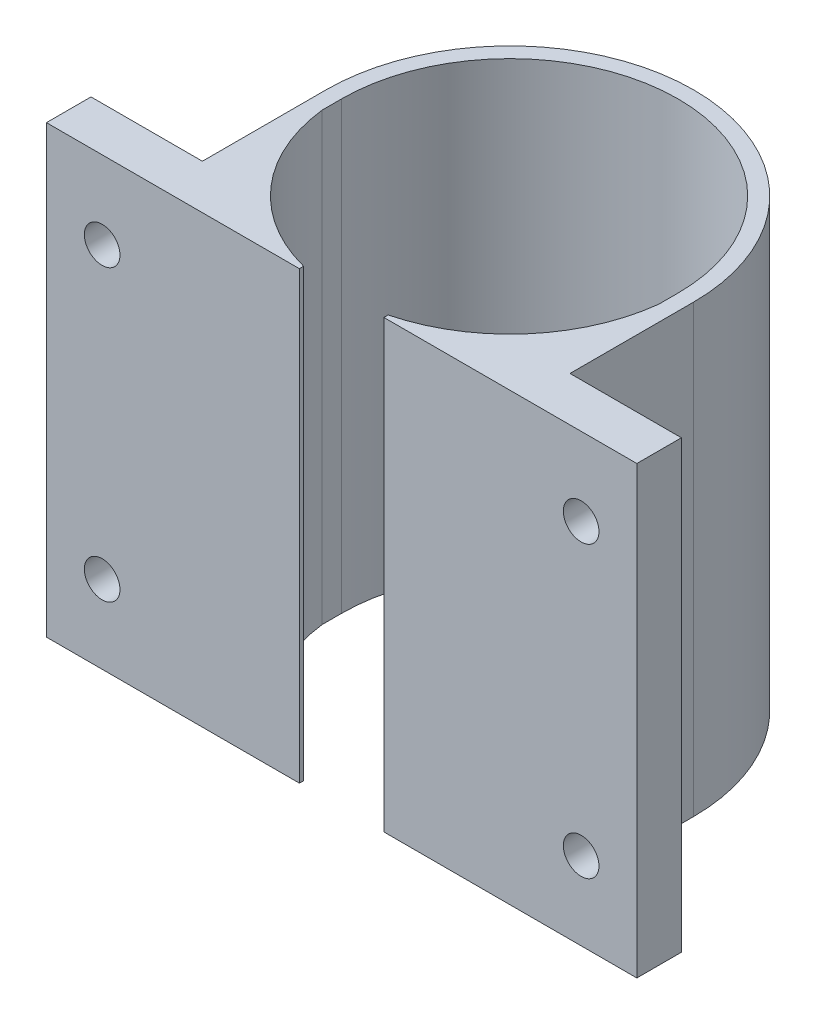
SolidWorks part; units mm, degrees
ref_plane "Front Plane" through (0, 0, 0) normal (0, 0, 1) x (1, 0, 0)
ref_plane "Top Plane" through (0, 0, 0) normal (0, 1, 0) x (1, 0, 0)
ref_plane "Right Plane" through (0, 0, 0) normal (1, 0, 0) x (0, 0, -1)
sketch "Sketch3" plane through (0, 0, 0) normal (0, 1, 0) x (1, 0, 0)
  line L0 (-16.5, 0) -> (-16.5, -15.1)
  line L2 (16.5, -15.1) -> (16.5, 0)
  line L3 (15.1, 0) -> (15.1, -15.1)
  line L4 (-15.1, 0) -> (-15.1, -15.1)
  line L5 (0, -15.1) -> (-16.5, -15.1)
  line L6 (-16.5, -15.1) -> (16.5, -15.1)
  arc A0 (15.1, 0) -> (-15.1, 0) centre (0, 0) ccw
  arc A1 (16.5, 0) -> (-16.5, 0) centre (0, 0) ccw
extrude "Boss-Extrude3" add sketch "Sketch3" along normal blind 40
sketch "Sketch8" plane through (16.5, 0, 0) normal (1, 0, 0) x (0, 0, -1)
  line L0 (-15.1, 40) -> (0, 40) construction
  line L1 (-15.1, 0) -> (-11.1, 0)
  line L2 (-15.1, 0) -> (-15.1, 40)
  line L3 (-15.1, 40) -> (-11.1, 40)
  line L4 (-11.1, 0) -> (-11.1, 40)
extrude "Boss-Extrude6" add sketch "Sketch8" along normal blind 10
sketch "Sketch9" plane through (-16.5, 0, 0) normal (-1, 0, 0) x (0, 0, 1)
  line L0 (0, 0) -> (15.1, 0) construction
  line L1 (15.1, 40) -> (11.1, 40)
  line L2 (15.1, 40) -> (15.1, 0)
  line L3 (15.1, 0) -> (11.1, 0)
  line L4 (11.1, 40) -> (11.1, 0)
extrude "Boss-Extrude7" add sketch "Sketch9" along normal blind 10
sketch "Sketch10" plane through (0, 0, 0) normal (0, -1, 0) x (-1, 0, 0)
  line L7 (15.1, -15.1) -> (15.1, -1.7407)
  line L9 (15.1, -15.1) -> (1.7407, -15.1)
  line L10 (3.7913, -15.1) -> (3.7913, -14.7196)
  line L11 (15.1, 0) -> (15.1, -15.1) construction
  line L12 (0, 0) -> (0, 15.1) construction
  line L13 (-3.7913, -15.1) -> (-3.7913, -14.7196)
  line L14 (-15.1, -15.1) -> (-1.7407, -15.1)
  line L15 (-15.1, -15.1) -> (-15.1, -1.7407)
  arc A1 (1.7407, -15.1) -> (15.1, -1.7407) centre (0, 0) ccw
  arc A2 (15.1, 0) -> (-15.1, 0) centre (0, 0) ccw construction
  arc A3 (-1.7407, -15.1) -> (-15.1, -1.7407) centre (0, 0) cw
extrude "Boss-Extrude9" add sketch "Sketch10" against normal blind 40 contours L13 A3 L10 L14 | A1 L10 L9 L13
sketch "Sketch11" plane through (0, 0, 11.1) normal (0, 0, -1) x (-1, 0, 0)
  line L0 (-21.5, 40) -> (-21.5, 0)
  line L1 (-26.5, 40) -> (-16.5, 40) construction
  line L2 (-26.5, 0) -> (-16.5, 0) construction
  line L3 (21.5, 40) -> (21.5, 0)
  line L4 (26.5, 40) -> (16.5, 40) construction
  line L5 (26.5, 0) -> (16.5, 0) construction
  circle A0 centre (-21.5, 33) radius 1.6
  circle A1 centre (-21.5, 7) radius 1.6
  circle A2 centre (21.5, 7) radius 1.6
  circle A3 centre (21.5, 33) radius 1.6
  dimension "D1" = 7
  dimension "D2" = 7
extrude "Cut-Extrude1" cut sketch "Sketch11" against normal blind 40 contours L0 A0 | L0 A1 | L0 A1 | L3 A2 | L3 A2 | L3 A3 | L3 A3
scale "Scale1" scale about origin uniform scaling no x scale factor 0.8 y scale factor 0.8 z scale factor 0.8
